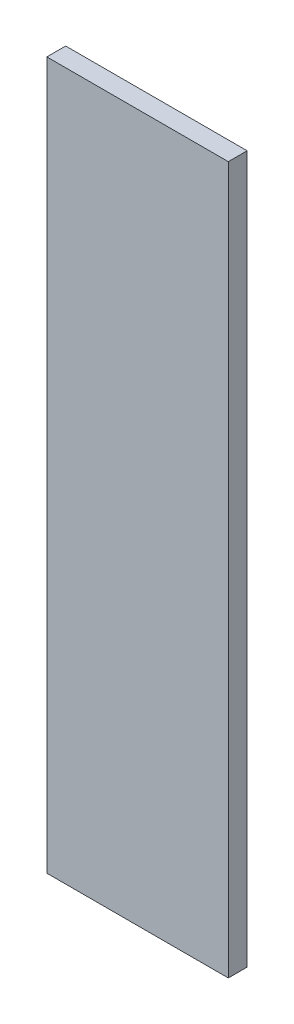
SolidWorks part; units mm, degrees
material "Gomma"
ref_plane "Piano frontale" through (0, 0, 0) normal (0, 0, 1) x (1, 0, 0)
ref_plane "Piano superiore" through (0, 0, 0) normal (0, 1, 0) x (1, 0, 0)
ref_plane "Piano destro" through (0, 0, 0) normal (1, 0, 0) x (0, 0, -1)
sketch "Schizzo1" plane through (0, 0, 0) normal (0, 0, 1) x (1, 0, 0)
  line L1 (3.85, -15) -> (-3.85, -15)
  line L2 (3.85, -15) -> (3.85, 15)
  line L3 (3.85, 15) -> (-3.85, 15)
  line L4 (-3.85, -15) -> (-3.85, 15)
  line L5 (3.85, -15) -> (-3.85, 15) construction
  line L6 (3.85, 15) -> (-3.85, -15) construction
  point P0 (0, 0)
  dimension "D1" = 7.7
  dimension "D2" = 30
extrude "Estrusione-Estrusione1" add sketch "Schizzo1" along normal blind 0.8
